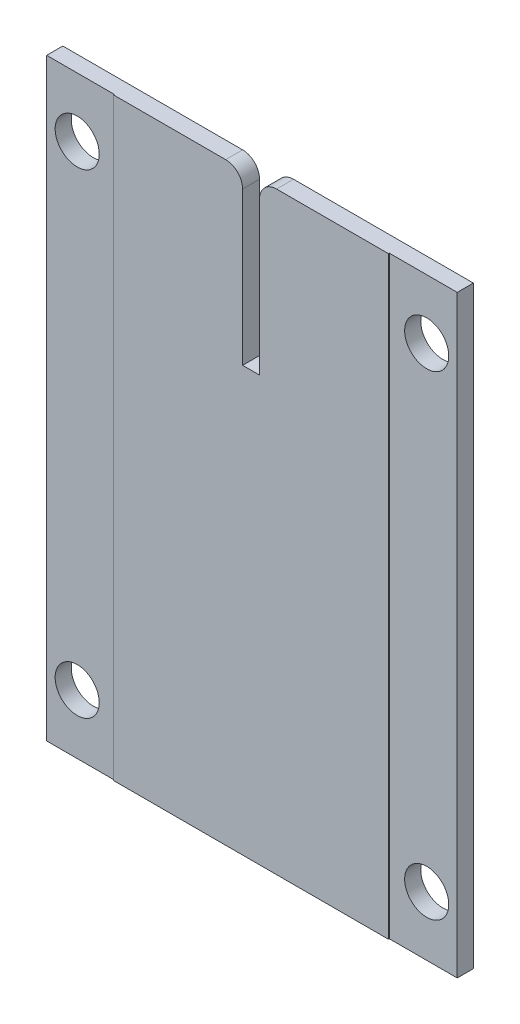
SolidWorks part; units mm, degrees
ref_plane "Front Plane" through (0, 0, 0) normal (0, 0, 1) x (1, 0, 0)
ref_plane "Top Plane" through (0, 0, 0) normal (0, 1, 0) x (1, 0, 0)
ref_plane "Right Plane" through (0, 0, 0) normal (1, 0, 0) x (0, 0, -1)
sketch "Sketch1" plane through (0, 0, 0) normal (0, 0, 1) x (1, 0, 0)
  line L1 (121, -175) -> (-121, -175)
  line L2 (121, -175) -> (121, 175)
  line L3 (121, 175) -> (-121, 175)
  line L4 (-121, -175) -> (-121, 175)
  line L5 (121, -175) -> (-121, 175) construction
  line L6 (121, 175) -> (-121, -175) construction
  circle A0 centre (-103, 140) radius 13
  circle A1 centre (-103, -140) radius 13
  circle A2 centre (103, 140) radius 13
  circle A3 centre (103, -140) radius 13
  point P0 (0, 0)
  dimension "D3" = 26
  dimension "D4" = 280
  dimension "D1" = 242
  dimension "D2" = 350
  dimension "D6" = 18
  dimension "D7" = 18
  dimension "D8" = 35
extrude "Boss-Extrude1" add sketch "Sketch1" along normal blind 10
sketch "Sketch2" plane through (0, 0, 10) normal (0, 0, 1) x (1, 0, 0)
  line L0 (-121, -175) -> (121, -175) construction
  line L1 (-121, 175) -> (-81, 175)
  line L4 (-121, 175) -> (-121, -175)
  line L5 (-121, -175) -> (-81, -175)
  line L6 (-81, 175) -> (-81, -175)
  line L8 (121, 175) -> (81, 175)
  line L9 (121, 175) -> (121, -175)
  line L10 (121, -175) -> (81, -175)
  line L11 (81, 175) -> (81, -175)
  dimension "D1" = 40
  dimension "D2" = 40
extrude "Cut-Extrude1" cut sketch "Sketch2" against normal blind 0.5
sketch "Sketch3" plane through (0, 0, 10) normal (0, 0, 1) x (1, 0, 0)
  line L0 (81, 175) -> (-81, 175) construction
  line L1 (-5, 75) -> (5, 75)
  line L2 (-5, 75) -> (-5, 175)
  line L3 (-5, 175) -> (5, 175)
  line L4 (5, 75) -> (5, 175)
  line L5 (-5, 75) -> (5, 175) construction
  line L6 (-5, 175) -> (5, 75) construction
  line L7 (-121, 175) -> (-121, -175) construction
  point P0 (0, 125)
  dimension "D1" = 121
  dimension "D2" = 100
  dimension "D3" = 10
extrude "Cut-Extrude2" cut sketch "Sketch3" against normal through all
fillet "Fillet1" radius 10 2 edges at (-5, 175, 5) (5, 175, 5)
